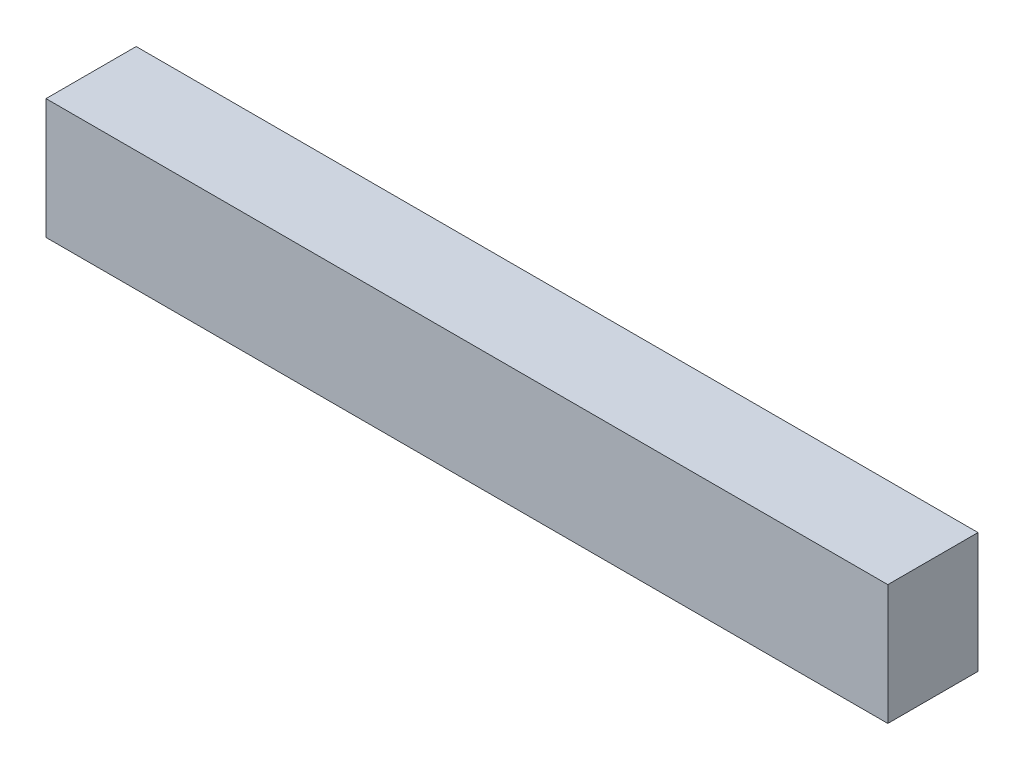
SolidWorks part; units mm, degrees
material "Custom Plastic"
ref_plane "Front Plane" through (0, 0, 0) normal (0, 0, 1) x (1, 0, 0)
ref_plane "Top Plane" through (0, 0, 0) normal (0, 1, 0) x (1, 0, 0)
ref_plane "Right Plane" through (0, 0, 0) normal (1, 0, 0) x (0, 0, -1)
sketch "Sketch1" plane through (0, 0, 0) normal (0, 0, 1) x (1, 0, 0)
  line L1 (-60.8405, -21.5548) -> (-32.8405, -21.5548)
  line L2 (-60.8405, -21.5548) -> (-60.8405, -17.5548)
  line L3 (-60.8405, -17.5548) -> (-32.8405, -17.5548)
  line L4 (-32.8405, -21.5548) -> (-32.8405, -17.5548)
  dimension "D1" = 28
  dimension "D2" = 4
extrude "Boss-Extrude1" add sketch "Sketch1" along normal blind 3
